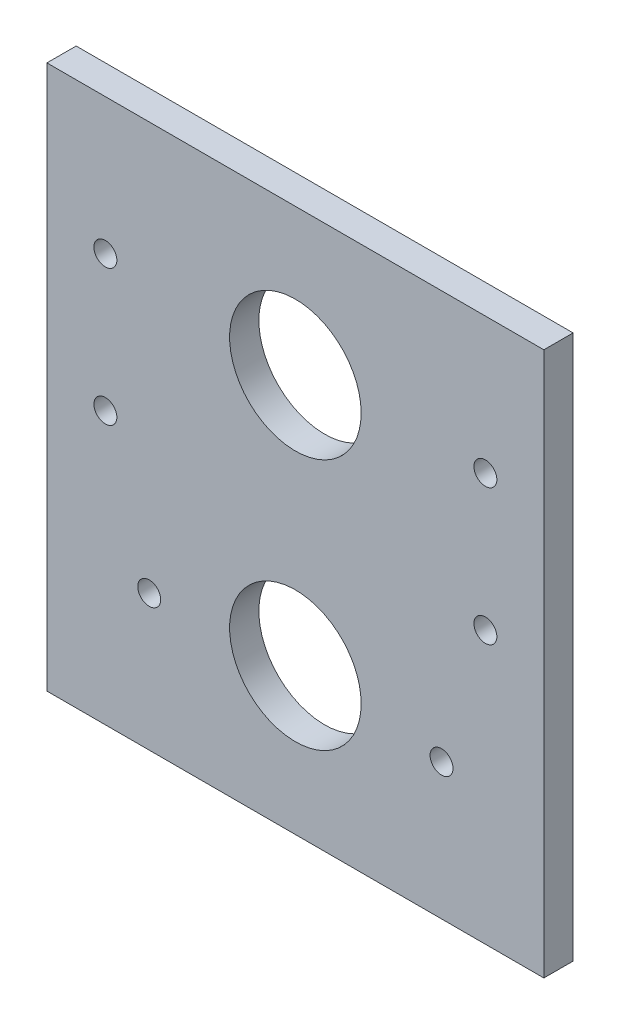
SolidWorks part; units mm, degrees
ref_plane "Front Plane" through (0, 0, 0) normal (0, 0, 1) x (1, 0, 0)
ref_plane "Top Plane" through (0, 0, 0) normal (0, 1, 0) x (1, 0, 0)
ref_plane "Right Plane" through (0, 0, 0) normal (1, 0, 0) x (0, 0, -1)
sketch "Sketch1" plane through (0, 0, 0) normal (0, 0, 1) x (1, 0, 0)
  line L0 (53.975, 118.1862) -> (53.975, 0) construction
  line L1 (0, 0) -> (107.95, 0)
  line L2 (0, 0) -> (0, 118.1862)
  line L3 (0, 118.1862) -> (107.95, 118.1862)
  line L4 (107.95, 0) -> (107.95, 118.1862)
  line L5 (12.7, 59.0931) -> (12.7, 118.1862) construction
  line L6 (12.7, 59.0931) -> (0, 59.0931) construction
  line L7 (95.25, 118.1862) -> (95.25, 59.0931) construction
  line L8 (95.25, 59.0931) -> (107.95, 59.0931) construction
  line L9 (12.7, 0) -> (12.7, 59.0931) construction
  line L10 (95.25, 59.0931) -> (95.25, 0) construction
  line L11 (12.7, 29.5465) -> (22.225, 29.5465) construction
  line L12 (95.25, 29.5466) -> (85.725, 29.5465) construction
  circle A0 centre (53.975, 86.4362) radius 14.2875
  circle A1 centre (53.975, 31.75) radius 14.2875
  circle A2 centre (95.25, 59.0931) radius 2.4892
  circle A3 centre (95.25, 88.6397) radius 2.4892
  circle A4 centre (12.7, 88.6396) radius 2.4892
  circle A5 centre (12.7, 59.0931) radius 2.4892
  circle A6 centre (22.225, 29.5465) radius 2.4892
  circle A7 centre (85.725, 29.5465) radius 2.4892
  circle A8 centre (53.975, 86.4362) radius 33.02 construction
  circle A9 centre (53.975, 31.75) radius 24.13 construction
  dimension "D1" = 28.575
  dimension "D2" = 28.575
  dimension "D3" = 54.6862
  dimension "D4" = 31.75
  dimension "D5" = 31.75
  dimension "D8" = 4.9784
  dimension "D10" = 66.04
  dimension "D11" = 48.26
  dimension "D6" = 12.7
  dimension "D7" = 53.975
  dimension "D9" = 9.525
extrude "Boss-Extrude1" add sketch "Sketch1" along normal blind 6.35
